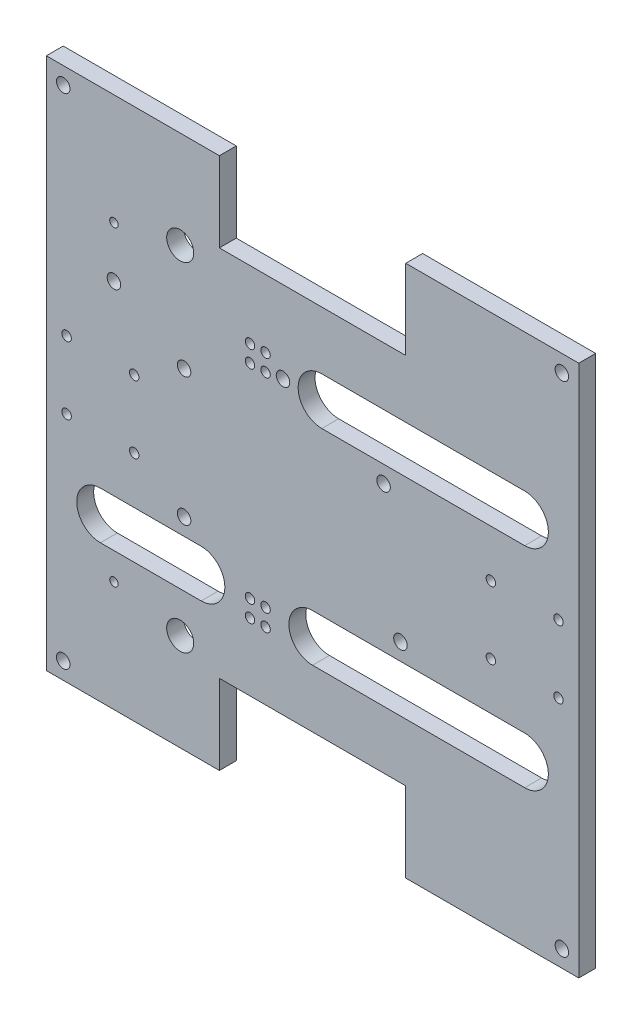
SolidWorks part; units mm, degrees
ref_plane "Front Plane" through (0, 0, 0) normal (0, 0, 1) x (1, 0, 0)
ref_plane "Top Plane" through (0, 0, 0) normal (0, 1, 0) x (1, 0, 0)
ref_plane "Right Plane" through (0, 0, 0) normal (1, 0, 0) x (0, 0, -1)
sketch "Sketch1" plane through (0, 0, 0) normal (0, 0, 1) x (1, 0, 0)
  line L5 (122.4099, 37.5406) -> (147.8099, 62.9406) construction
  line L6 (346.701, 12.7177) -> (504.181, 12.7177) construction
  line L11 (214.7899, 120.2406) -> (214.7899, -19.7594) construction
  line L12 (307.1699, 37.5406) -> (305.9126, 38.7978) construction
  line L16 (283.0271, 61.6833) -> (281.7699, 62.9406) construction
  line L17 (197.1369, 5.6406) -> (191.2949, 11.9906) construction
  line L22 (135.1099, 10.8706) -> (294.4699, 10.8706) construction
  line L23 (135.1099, 19.7606) -> (172.9532, 19.7606)
  line L28 (135.1099, 1.9806) -> (172.9532, 1.9806)
  line L29 (218.2699, 89.6106) -> (294.4699, 89.6106) construction
  line L30 (346.701, 12.7177) -> (346.701, -43.1623) construction
  line L31 (346.701, -43.1623) -> (504.181, -43.1623) construction
  line L32 (504.181, 12.7177) -> (504.181, -43.1623) construction
  line L33 (151.2899, 76.9106) -> (252.8899, 76.9106) construction
  line L34 (151.2899, 76.9106) -> (151.2899, 23.5706) construction
  line L35 (151.2899, 23.5706) -> (252.8899, 23.5706) construction
  line L36 (252.8899, 76.9106) -> (252.8899, 23.5706) construction
  line L37 (249.7899, 150.2406) -> (314.7899, 150.2406)
  line L38 (114.7899, 150.2406) -> (179.7899, 150.2406)
  line L39 (114.7899, 150.2406) -> (114.7899, -49.7594)
  line L40 (114.7899, -49.7594) -> (179.7899, -49.7594)
  line L41 (314.7899, 150.2406) -> (314.7899, -49.7594)
  line L43 (179.7899, 150.2406) -> (179.7899, 120.2406)
  line L44 (179.7899, 120.2406) -> (249.7899, 120.2406)
  line L45 (249.7899, 150.2406) -> (249.7899, 120.2406)
  line L46 (114.7899, 50.2406) -> (314.7899, 50.2406) construction
  line L47 (249.7899, -49.7594) -> (249.7899, -19.7594)
  line L48 (179.7899, -19.7594) -> (249.7899, -19.7594)
  line L49 (179.7899, -49.7594) -> (179.7899, -19.7594)
  line L50 (249.7899, -49.7594) -> (314.7899, -49.7594)
  line L51 (218.2699, 98.5006) -> (294.4699, 98.5006)
  line L52 (218.2699, 80.7206) -> (294.4699, 80.7206)
  line L53 (214.7899, 1.9806) -> (294.4699, 1.9806)
  line L54 (214.7899, 19.7606) -> (294.4699, 19.7606)
  circle A1 centre (140.1899, -8.1794) radius 1.5875
  circle A2 centre (122.4099, 62.9406) radius 1.778
  circle A3 centre (122.4099, 37.5406) radius 1.778
  circle A4 centre (147.8099, 37.5406) radius 1.778
  circle A5 centre (140.1899, 108.6606) radius 1.5875
  circle A6 centre (147.8099, 62.9406) radius 1.778
  circle A9 centre (281.7699, 62.9406) radius 1.778
  circle A10 centre (307.1699, 62.9406) radius 1.778
  circle A11 centre (281.7699, 37.5406) radius 1.778
  circle A12 centre (307.1699, 37.5406) radius 1.778
  circle A13 centre (121.1399, 143.8906) radius 2.54
  circle A14 centre (140.1899, 89.5972) radius 2.54
  circle A15 centre (203.6899, 89.5972) radius 2.54
  circle A16 centre (191.2949, 11.9906) radius 1.778
  circle A17 centre (197.1369, 11.9906) radius 1.778
  circle A18 centre (191.2949, 5.6406) radius 1.778
  circle A19 centre (197.1369, 5.6406) radius 1.778
  circle A20 centre (191.2949, 94.8406) radius 1.778
  circle A21 centre (191.2949, 88.4906) radius 1.778
  circle A22 centre (197.1369, 88.4906) radius 1.778
  circle A23 centre (197.1369, 94.8406) radius 1.778
  circle A24 centre (166.5299, 74.3706) radius 2.54
  circle A25 centre (241.4599, 74.3706) radius 2.54
  circle A26 centre (166.5299, 26.1106) radius 2.54
  circle A27 centre (247.8099, 26.1106) radius 2.54
  circle A28 centre (121.1399, -43.4094) radius 2.54
  circle A29 centre (308.4399, -43.4094) radius 2.54
  circle A30 centre (308.4399, 143.8906) radius 2.54
  arc A31 (135.1099, 19.7606) -> (135.1099, 1.9806) centre (135.1099, 10.8706) ccw
  arc A32 (294.4699, 1.9806) -> (294.4699, 19.7606) centre (294.4699, 10.8706) ccw
  arc A33 (218.2699, 98.5006) -> (218.2699, 80.7206) centre (218.2699, 89.6106) ccw
  arc A34 (294.4699, 80.7206) -> (294.4699, 98.5006) centre (294.4699, 89.6106) ccw
  circle A35 centre (165.0767, 113.7406) radius 5.08
  circle A36 centre (165.0767, -13.2594) radius 5.08
  arc A37 (172.9532, 1.9806) -> (172.9532, 19.7606) centre (172.9532, 10.8706) ccw
  arc A38 (214.7899, 19.7606) -> (214.7899, 1.9806) centre (214.7899, 10.8706) ccw
  point P0 (0, 0)
  point P1 (135.1099, 50.2406)
  point P31 (194.2159, 8.8156)
  point P36 (214.7899, 10.8706)
  point P94 (256.3699, 89.6106)
  dimension "D12" = 20.32
  dimension "D13" = 25.4
  dimension "D19" = 25.4
  dimension "D26" = 3.556
  dimension "D27" = 3.556
  dimension "D30" = 3.556
  dimension "D14" = 5.08
  dimension "D17" = 5.08
  dimension "D18" = 5.08
  dimension "D33" = 3.556
  dimension "D34" = 5.842
  dimension "D39" = 3.556
  dimension "D44" = 5.08
  dimension "D48" = 5.08
  dimension "D49" = 5.08
  dimension "D50" = 8.89
  dimension "D55" = 8.89
  dimension "D58" = 10.16
  dimension "D4" = 58.42
  dimension "D5" = 12.7
  dimension "D8" = 157.48
  dimension "D9" = 55.88
  dimension "D10" = 101.6
  dimension "D11" = 53.34
  dimension "D15" = 6.35
  dimension "D16" = 6.35
  dimension "D20" = 200
  dimension "D21" = 200
  dimension "D22" = 30
  dimension "D23" = 70
  dimension "D24" = 65
  dimension "D25" = 0
  dimension "D28" = 25.4
  dimension "D29" = 0
  dimension "D6" = 0
  dimension "D7" = 0
  dimension "D31" = 63.5
  dimension "D32" = 25.4
  dimension "D35" = 6.35
  dimension "D36" = 6.35
  dimension "D37" = 20.574
  dimension "D38" = 25.4
  dimension "D40" = 26.67
  dimension "D41" = 63.5
  dimension "D42" = 2.54
  dimension "D43" = 15.24
  dimension "D45" = 74.93
  dimension "D46" = 81.28
  dimension "D47" = 0
  dimension "D51" = 39.37
  dimension "D52" = 20.32
  dimension "D53" = 20.32
  dimension "D54" = 39.37
  dimension "D56" = 20.32
  dimension "D57" = 76.2
  dimension "D59" = 25.4
  dimension "D60" = 63.5
extrude "Boss-Extrude1" add sketch "Sketch1" along normal blind 6.35
